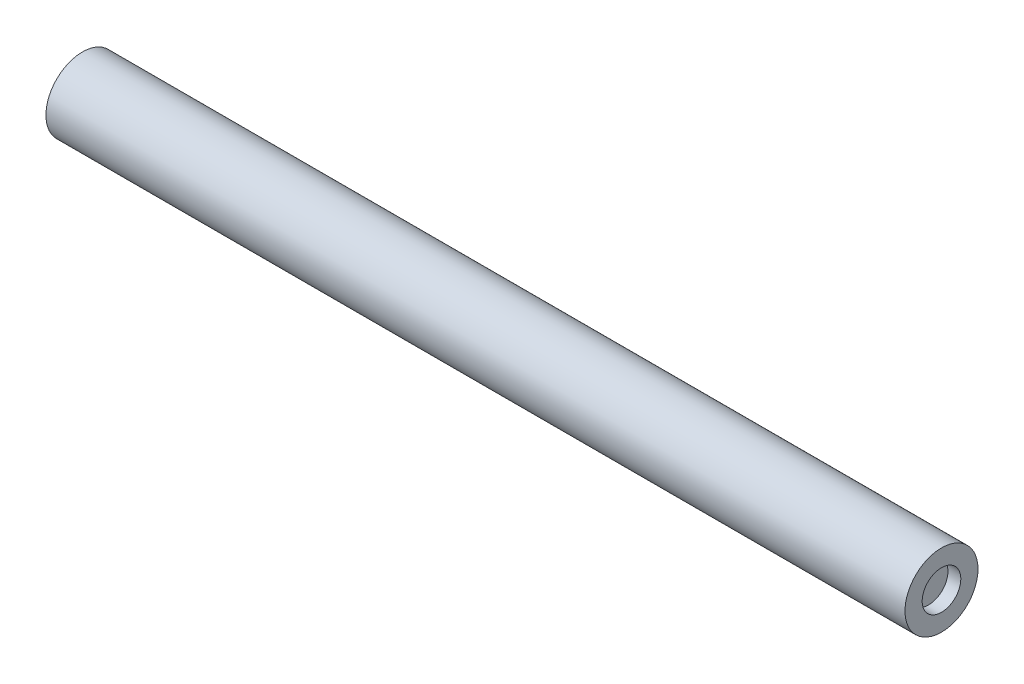
SolidWorks part; units mm, degrees
ref_plane "Front Plane" through (0, 0, 0) normal (0, 0, 1) x (1, 0, 0)
ref_plane "Top Plane" through (0, 0, 0) normal (0, 1, 0) x (1, 0, 0)
ref_plane "Right Plane" through (0, 0, 0) normal (1, 0, 0) x (0, 0, -1)
sketch "Sketch1" plane through (0, 0, 0) normal (1, 0, 0) x (0, 0, -1)
  circle A1 centre (0, 0) radius 8.636
extrude "Boss-Extrude1" add sketch "Sketch1" along normal blind 203.2
sketch "Sketch2" plane through (203.2, 0, 0) normal (1, 0, 0) x (0, 0, -1)
  circle A0 centre (0, 0) radius 4.572
extrude "Cut-Extrude1" cut sketch "Sketch2" against normal blind 3.048
sketch "Sketch3" plane through (0, 0, 0) normal (-1, 0, 0) x (0, 0, 1)
  circle A0 centre (0, 0) radius 2.794
extrude "Cut-Extrude2" cut sketch "Sketch3" against normal blind 14.478 contours A0
